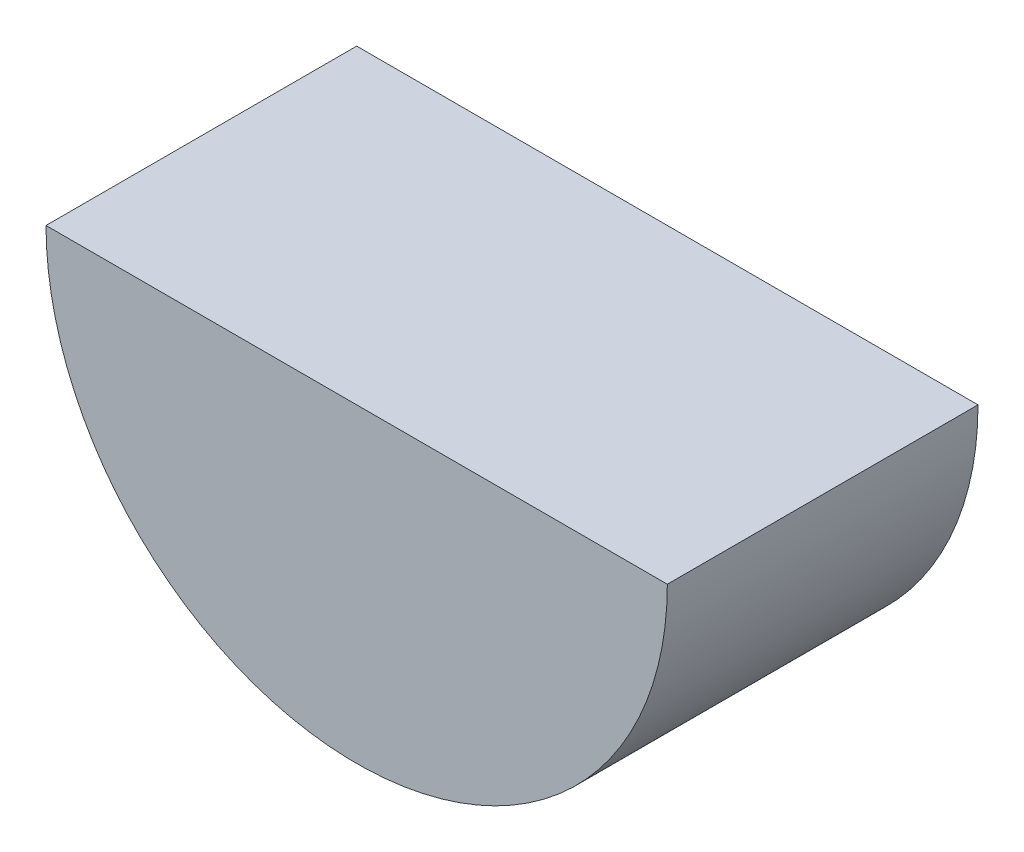
SolidWorks part; units mm, degrees
material "Rubber"
ref_plane "Front Plane" through (0, 0, 0) normal (0, 0, 1) x (1, 0, 0)
ref_plane "Top Plane" through (0, 0, 0) normal (0, 1, 0) x (1, 0, 0)
ref_plane "Right Plane" through (0, 0, 0) normal (1, 0, 0) x (0, 0, -1)
sketch "Sketch2" plane through (0, 0, 0) normal (0, 0, 1) x (1, 0, 0)
  line L0 (-15, 0) -> (15, 0)
  arc A0 (-15, 0) -> (15, 0) centre (0, 0) ccw
  dimension "D1" = 30
extrude "Boss-Extrude1" add sketch "Sketch2" along normal mid plane 15
